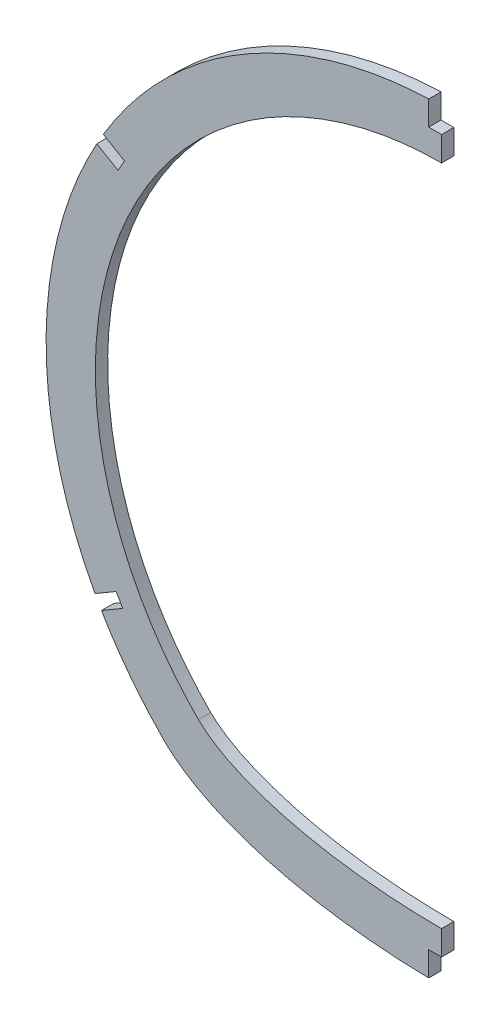
SolidWorks part; units mm, degrees
material "Plywood"
ref_plane "Front Plane" through (0, 0, 0) normal (0, 0, 1) x (1, 0, 0)
ref_plane "Top Plane" through (0, 0, 0) normal (0, 1, 0) x (1, 0, 0)
ref_plane "Right Plane" through (0, 0, 0) normal (1, 0, 0) x (0, 0, -1)
sketch "Sketch2" plane through (0, 0, 0) normal (0, 0, 1) x (1, 0, 0)
  spline S0 degree 3 poles (2568.0953, -4090.4659) (-4057.024, 3451.1389) (4945.1528, -1980.2124) (-4825.8731, 402.3844) knots -545.10296 -545.10296 -545.10296 -545.10296 547.49362 547.49362 547.49362 547.49362 only from (49.5009, 91.348) to (50.6103, 90.7129)
  spline S1 degree 3 poles (3341.4723, -3725.6669) (-100.6677, -22.1088) (-50.1916, -95.8099) (-74.4696, -70.0026) (-75.8372, -68.488) (-77.1861, -66.9319) (-78.5157, -65.3347) (-79.8244, -63.6962) (-81.5476, -61.4464) (-83.6416, -58.5297) (-85.6296, -55.5014) (-87.1622, -52.9973) (-88.2859, -51.0701) (-90.1147, -47.7724) (-92.5499, -42.8914) (-95.3516, -36.1752) (-97.8068, -28.8548) (-99.4166, -22.4927) (-100.4844, -16.9735) (-101.2174, -12.1158) (-101.8059, -6.1085) (-102.0556, 1.0556) (-101.6376, 11.9166) (-99.5817, 24.7034) (-94.9478, 39.4776) (-88.6565, 52.7081) (-80.0434, 65.5541) (-69.8712, 76.7554) (-58.637, 85.9148) (-47.202, 92.899) (-35.7905, 98.0522) (-24.0008, 101.7167) (-12.0295, 103.8942) (-3.6569, 104.3953) (0.9911, 104.3723) (2.6447, 104.3478) (5.2959, 104.2559) (8.9441, 104.0024) (12.9235, 103.5662) (16.8979, 102.9692) (20.8607, 102.2106) (24.805, 101.2899) (28.7242, 100.207) (32.6113, 98.9619) (36.4593, 97.5551) (39.9429, 96.1186) (42.4433, 94.9816) (43.9946, 94.2376) (44.9225, 93.7809) (45.8466, 93.3143) (46.7667, 92.8378) (47.6827, 92.3514) (70.4007, 80.003) (151.5153, 23.3747) (-4363.3748, 2440.7113) knots -0.313173 -0.313173 -0.313173 -0.313173 0.006795 0.013654 0.020575 0.02756 0.034609 0.041722 0.048899 0.063446 0.078252 0.085753 0.09332 0.100952 0.124124 0.148785 0.174948 0.202627 0.215494 0.232144 0.2526 0.276886 0.305032 0.363116 0.408011 0.462235 0.511576 0.564908 0.615598 0.658549 0.700916 0.742691 0.78387 0.82445 0.827809 0.831171 0.841279 0.854802 0.868378 0.882008 0.895692 0.909428 0.923217 0.93706 0.950955 0.964902 0.975398 0.978902 0.982411 0.985922 0.989437 0.992954 0.996476 1.262403 1.262403 1.262403 1.262403 only from (-71.6774, -72.9104) to (49.5009, 91.348)
  spline S2 degree 3 poles (-71.6774, -72.9104) (-72.1092, -72.4767) (-72.9729, -71.5936) (-74.4696, -70.0026) (-75.8372, -68.488) (-77.1861, -66.9319) (-78.5157, -65.3347) (-79.8244, -63.6962) (-81.5476, -61.4464) (-83.6416, -58.5297) (-85.6296, -55.5014) (-87.1622, -52.9973) (-88.2859, -51.0701) (-90.1147, -47.7724) (-92.5499, -42.8914) (-95.3516, -36.1752) (-97.8068, -28.8548) (-99.4166, -22.4927) (-100.4844, -16.9735) (-101.2174, -12.1158) (-101.8059, -6.1085) (-102.0556, 1.0556) (-101.6376, 11.9166) (-99.5817, 24.7034) (-94.9478, 39.4776) (-88.6565, 52.7081) (-80.0434, 65.5541) (-69.8712, 76.7554) (-58.637, 85.9148) (-47.202, 92.899) (-35.7905, 98.0522) (-24.0008, 101.7167) (-12.0295, 103.8942) (-3.6569, 104.3953) (0.9911, 104.3723) (2.6447, 104.3478) (5.2959, 104.2559) (8.9441, 104.0024) (12.9235, 103.5662) (16.8979, 102.9692) (20.8607, 102.2106) (24.805, 101.2899) (28.7242, 100.207) (32.6113, 98.9619) (36.4593, 97.5551) (39.9429, 96.1186) (42.4433, 94.9816) (43.9946, 94.2376) (44.9225, 93.7809) (45.8466, 93.3143) (46.7667, 92.8378) (47.6827, 92.3514) (48.5618, 91.8735) (49.1883, 91.5244) (49.5009, 91.348) knots 0 0 0 0 0.006795 0.013654 0.020575 0.02756 0.034609 0.041722 0.048899 0.063446 0.078252 0.085753 0.09332 0.100952 0.124124 0.148785 0.174948 0.202627 0.215494 0.232144 0.2526 0.276886 0.305032 0.363116 0.408011 0.462235 0.511576 0.564908 0.615598 0.658549 0.700916 0.742691 0.78387 0.82445 0.827809 0.831171 0.841279 0.854802 0.868378 0.882008 0.895692 0.909428 0.923217 0.93706 0.950955 0.964902 0.975398 0.978902 0.982411 0.985922 0.989437 0.992954 0.996476 1 1 1 1
  spline S3 degree 3 poles (49.5009, 91.348) (49.872, 91.1385) (50.2418, 90.9268) (50.6103, 90.7129) knots 0 0 0 0 1 1 1 1
  spline S4 degree 3 poles (-4193.7763, 2732.8048) (81.5381, 53.7028) (23.1515, 107.7521) (53.9325, 88.7036) (55.5798, 87.6387) (57.2181, 86.5331) (58.847, 85.3874) (60.4652, 84.2011) (62.6149, 82.559) (65.2687, 80.4032) (68.3802, 77.661) (71.4204, 74.7537) (74.3792, 71.6812) (77.2464, 68.4441) (79.5428, 65.6199) (81.3243, 63.2803) (82.6352, 61.4798) (83.9151, 59.6395) (85.6826, 56.9767) (87.8969, 53.3695) (90.4626, 48.6769) (92.8892, 43.6261) (95.1327, 38.2157) (97.1465, 32.4482) (98.8821, 26.3306) (100.2892, 19.8751) (101.2586, 13.4739) (101.8173, 7.2467) (102.0152, 1.305) (101.8786, -4.6242) (101.3926, -10.7347) (100.5371, -16.8676) (99.3294, -22.8638) (97.8936, -28.3722) (96.657, -32.2698) (95.7856, -34.7444) (95.046, -36.7643) (93.9532, -39.5358) (92.4358, -43.007) (90.8217, -46.3649) (89.1186, -49.6082) (87.3342, -52.7363) (85.4757, -55.7486) (83.5505, -58.6453) (81.5655, -61.4266) (79.3077, -64.3807) (77.437, -66.6472) (76.0073, -68.2889) (75.2951, -69.0897) (74.579, -69.8782) (73.8594, -70.6545) (73.1363, -71.4184) (59.0939, -85.9325) (120.7935, -16.6257) (-3396.6628, -3673.2191) knots -0.504739 -0.504739 -0.504739 -0.504739 0.010157 0.020393 0.030709 0.041103 0.051576 0.062128 0.072758 0.094254 0.116062 0.138181 0.16061 0.183347 0.206391 0.218027 0.22974 0.241529 0.253393 0.280162 0.30828 0.337739 0.36853 0.400644 0.434071 0.4688 0.504821 0.536145 0.567394 0.59857 0.62967 0.664059 0.696204 0.726123 0.75383 0.760691 0.767516 0.787768 0.807688 0.827278 0.84654 0.865477 0.884089 0.902378 0.920346 0.937994 0.961032 0.966703 0.97234 0.977942 0.983508 0.98904 0.994538 1.266327 1.266327 1.266327 1.266327 only from (50.6103, 90.7129) to (71.6784, -72.9104)
  spline S5 degree 3 poles (50.6103, 90.7129) (51.1284, 90.4118) (52.1672, 89.796) (53.9325, 88.7036) (55.5798, 87.6387) (57.2181, 86.5331) (58.847, 85.3874) (60.4652, 84.2011) (62.6149, 82.559) (65.2687, 80.4032) (68.3802, 77.661) (71.4204, 74.7537) (74.3792, 71.6812) (77.2464, 68.4441) (79.5428, 65.6199) (81.3243, 63.2803) (82.6352, 61.4798) (83.9151, 59.6395) (85.6826, 56.9767) (87.8969, 53.3695) (90.4626, 48.6769) (92.8892, 43.6261) (95.1327, 38.2157) (97.1465, 32.4482) (98.8821, 26.3306) (100.2892, 19.8751) (101.2586, 13.4739) (101.8173, 7.2467) (102.0152, 1.305) (101.8786, -4.6242) (101.3926, -10.7347) (100.5371, -16.8676) (99.3294, -22.8638) (97.8936, -28.3722) (96.657, -32.2698) (95.7856, -34.7444) (95.046, -36.7643) (93.9532, -39.5358) (92.4358, -43.007) (90.8217, -46.3649) (89.1186, -49.6082) (87.3342, -52.7363) (85.4757, -55.7486) (83.5505, -58.6453) (81.5655, -61.4266) (79.3077, -64.3807) (77.437, -66.6472) (76.0073, -68.2889) (75.2951, -69.0897) (74.579, -69.8782) (73.8594, -70.6545) (73.1363, -71.4184) (72.3175, -72.2647) (71.8912, -72.6967) (71.6784, -72.9104) knots 0 0 0 0 0.010157 0.020393 0.030709 0.041103 0.051576 0.062128 0.072758 0.094254 0.116062 0.138181 0.16061 0.183347 0.206391 0.218027 0.22974 0.241529 0.253393 0.280162 0.30828 0.337739 0.36853 0.400644 0.434071 0.4688 0.504821 0.536145 0.567394 0.59857 0.62967 0.664059 0.696204 0.726123 0.75383 0.760691 0.767516 0.787768 0.807688 0.827278 0.84654 0.865477 0.884089 0.902378 0.920346 0.937994 0.961032 0.966703 0.97234 0.977942 0.983508 0.98904 0.994538 1 1 1 1
  spline S6 degree 3 poles (-4835.9061, 806.008) (5645.7753, -391.3089) (-5645.7177, -391.3145) (4835.7602, 805.9912) knots -2.930767 -2.930767 -2.930767 -2.930767 3.930735 3.930735 3.930735 3.930735 weights 1 1 1 1 only from (71.6784, -72.9104) to (-71.6774, -72.9104)
  spline S7 degree 3 poles (71.6784, -72.9104) (46.3599, -98.3417) (-46.3589, -98.3417) (-71.6774, -72.9104) knots 0 0 0 0 1 1 1 1 weights 1 1 1 1
  spline S8 degree 1 poles (-62.6772, -63.9502) (43.2582, 80.2883) knots 0 0 1 1 construction
  spline S9 degree 1 poles (43.2582, 80.2883) (44.2327, 79.7303) knots 0 0 1 1 construction
  spline S10 degree 1 poles (44.2327, 79.7303) (62.6782, -63.9502) knots 0 0 1 1 construction
  spline S11 degree 1 poles (62.6782, -63.9502) (-62.6772, -63.9502) knots 0 0 1 1 construction
  spline S12 degree 3 poles (-62.6772, -63.9502) (-62.8955, -63.7309) (-63.3217, -63.2983) (-64.0021, -62.5921) (-64.7538, -61.7946) (-65.7039, -60.7646) (-66.8046, -59.5274) (-68.5568, -57.4681) (-70.6482, -54.8355) (-73.8114, -50.469) (-77.3945, -44.7561) (-82.3029, -35.1354) (-86.8108, -22.36) (-90.3543, -0.9674) (-87.6499, 26.3501) (-73.3334, 55.9721) (-49.624, 78.7088) (-24.4872, 89.3835) (-3.091, 92.1159) (13.039, 91.1975) (26.1203, 87.9966) (34.8794, 84.5248) (39.1021, 82.5104) (41.2143, 81.4108) (42.347, 80.7976) (42.9592, 80.4569) (43.2582, 80.2883) knots 0 0 0 0 0.003906 0.007812 0.011719 0.015625 0.023437 0.03125 0.046875 0.062499 0.093749 0.124999 0.187498 0.249998 0.374997 0.499996 0.624995 0.749994 0.812493 0.874993 0.937492 0.968742 0.984367 0.992179 0.996085 0.999992 0.999992 0.999992 0.999992
  spline S13 degree 3 poles (43.2582, 80.2883) (43.3397, 80.2423) (43.5025, 80.15) (43.7464, 80.0108) (43.9898, 79.871) (44.1518, 79.7773) (44.2327, 79.7303) knots 0.002022 0.002022 0.002022 0.002022 0.251014 0.500005 0.748996 0.997987 0.997987 0.997987 0.997987
  spline S14 degree 3 poles (44.2327, 79.7303) (44.5844, 79.526) (45.2596, 79.1276) (46.4154, 78.4223) (47.5738, 77.6928) (49.0079, 76.7584) (50.8048, 75.5306) (53.6072, 73.4932) (57.0034, 70.7903) (64.7641, 63.8421) (74.8536, 51.7693) (84.3118, 33.0007) (89.3026, 12.5818) (89.5941, -8.4639) (85.1673, -29.0225) (78.4712, -43.2887) (72.7378, -52.0045) (70.1455, -55.4923) (67.9548, -58.1887) (66.5372, -59.8344) (65.3768, -61.1241) (64.6361, -61.9238) (64.0489, -62.544) (63.5408, -63.0721) (63.0657, -63.5594) (62.8132, -63.8146) (62.6782, -63.9502) knots 0.000015 0.000015 0.000015 0.000015 0.007827 0.015639 0.023452 0.031264 0.046889 0.062514 0.093763 0.125013 0.250011 0.375009 0.500007 0.625005 0.750004 0.875002 0.906251 0.937501 0.953126 0.96875 0.976563 0.984375 0.988281 0.992188 0.996094 1 1 1 1
  spline S15 degree 3 poles (62.6782, -63.9502) (62.4421, -64.1873) (61.9735, -64.6322) (60.8483, -65.5949) (59.1789, -66.8259) (56.7375, -68.3252) (52.9423, -70.2888) (47.261, -72.5995) (39.2215, -74.978) (30.229, -76.8801) (17.3048, -78.7217) (0.0005, -79.6587) (-17.3038, -78.7217) (-30.228, -76.8801) (-39.2204, -74.978) (-47.2599, -72.5995) (-52.9413, -70.2888) (-56.7364, -68.3252) (-59.1779, -66.8259) (-60.8473, -65.5949) (-61.9724, -64.6322) (-62.4411, -64.1873) (-62.6772, -63.9502) knots 0 0 0 0 0.015625 0.03125 0.0625 0.09375 0.125 0.1875 0.25 0.3125 0.375 0.5 0.625 0.6875 0.75 0.8125 0.875 0.90625 0.9375 0.96875 0.984375 1 1 1 1
  dimension "D1" = 12.7
extrude "Boss-Extrude1" add sketch "Sketch2" against normal blind 3.175
sketch "Sketch3" plane through (0, 0, 0) normal (1, 0, 0) x (0, 0, -1)
  line L1 (-61.0107, 158.0584) -> (68.3789, 158.0584)
  line L2 (-61.0107, 158.0584) -> (-61.0107, -136.6623)
  line L3 (-61.0107, -136.6623) -> (68.3789, -136.6623)
  line L4 (68.3789, 158.0584) -> (68.3789, -136.6623)
extrude "Cut-Extrude1" cut sketch "Sketch3" along normal through all
sketch "Sketch4" plane through (0, 0, -3.175) normal (0, 0, -1) x (-1, 0, 0)
  line L0 (0, 0) -> (0, 91.6752) construction
  line L1 (0, 91.6752) -> (0, 98.0252) construction
  line L2 (0, 98.0252) -> (3.302, 98.0252)
  line L3 (0, 98.0252) -> (0, 110.7252)
  line L4 (3.302, 98.0252) -> (3.302, 110.7252)
  line L5 (0, 110.7252) -> (3.302, 110.7252)
  line L6 (77.1004, 46.575) -> (82.577, 49.789) construction
  line L10 (81.7221, 51.2458) -> (83.4319, 48.3323)
  line L11 (77.1004, 46.575) -> (0, 1.327) construction
  line L12 (81.7221, 51.2458) -> (92.6752, 57.6738)
  line L13 (83.4319, 48.3323) -> (94.385, 54.7603)
  line L14 (92.6752, 57.6738) -> (94.385, 54.7603)
  line L21 (77.572, -44.1978) -> (83.0486, -47.4118) construction
  line L22 (77.572, -44.1978) -> (0, 1.327) construction
  line L23 (82.1936, -48.8686) -> (83.9035, -45.955)
  line L24 (82.1936, -48.8686) -> (93.1467, -55.2966)
  line L25 (83.9035, -45.955) -> (94.8566, -52.3831)
  line L26 (93.1467, -55.2966) -> (94.8566, -52.3831)
  line L27 (0, 1.327) -> (0, -79.2839) construction
  line L28 (0, -91.9839) -> (0, -79.2839) construction
  line L29 (0, -79.2839) -> (0, -85.6339) construction
  line L30 (0, -85.6339) -> (3.302, -85.6339)
  line L31 (0, -85.6339) -> (0, -98.3339)
  line L32 (3.302, -85.6339) -> (3.302, -98.3339)
  line L33 (0, -98.3339) -> (3.302, -98.3339)
  point P17 (83.0486, -47.4118)
  dimension "D13" = 6.35
  dimension "D1" = 6.35
  dimension "D2" = 91.6752
  dimension "D3" = 3.302
  dimension "D4" = 12.7
  dimension "D5" = 59.593
  dimension "D6" = 1.327
  dimension "D7" = 89.3972
  dimension "D8" = 6.35
  dimension "D9" = 3.3782
  dimension "D10" = 12.7
  dimension "D11" = 59.593
  dimension "D12" = 89.944
  dimension "D14" = 3.3782
  dimension "D15" = 12.7
  dimension "D16" = 6.35
  dimension "D17" = 80.6109
  dimension "D18" = 3.302
  dimension "D19" = 12.7
extrude "Cut-Extrude2" cut sketch "Sketch4" against normal through all
